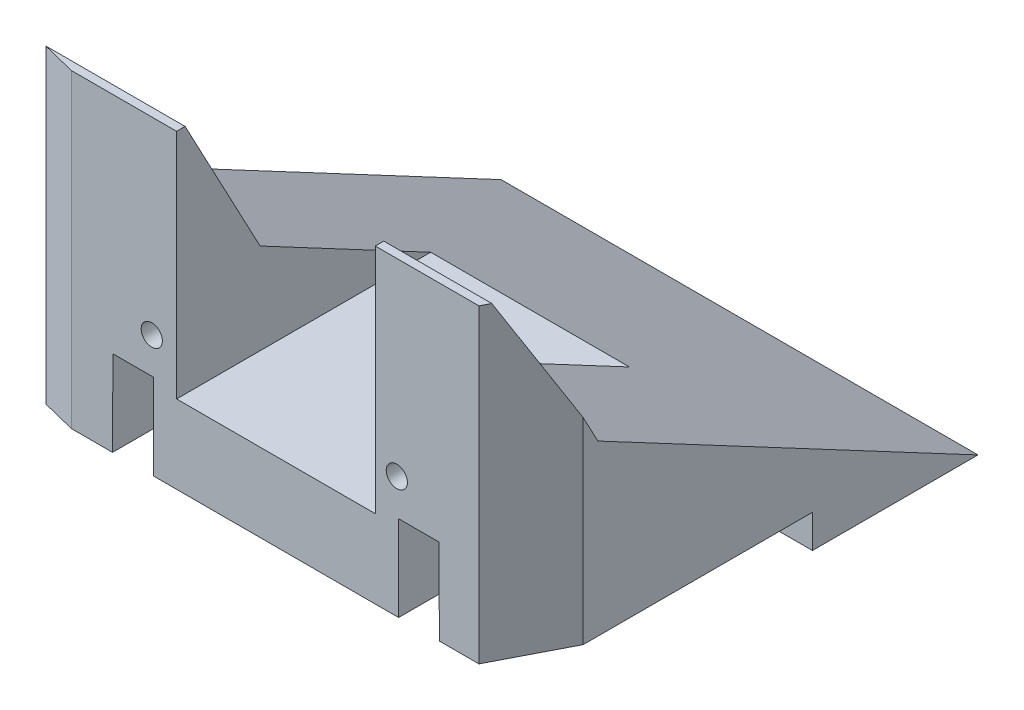
SolidWorks part; units mm, degrees
ref_plane "Alzado" through (0, 0, 0) normal (0, 0, 1) x (1, 0, 0)
ref_plane "Planta" through (0, 0, 0) normal (0, 1, 0) x (1, 0, 0)
ref_plane "Vista lateral" through (0, 0, 0) normal (1, 0, 0) x (0, 0, -1)
sketch "Croquis1" plane through (0, 0, 0) normal (1, 0, 0) x (0, 0, -1)
  line L1 (0, 0) -> (70, 0)
  line L2 (0, 0) -> (0, 51.82)
  line L3 (0, 51.82) -> (70, 51.82)
  line L4 (70, 0) -> (70, 51.82)
  dimension "D1" = 51.82
  dimension "D2" = 70
extrude "Saliente-Extruir1" add sketch "Croquis1" along normal blind 72
sketch "Croquis4" plane through (72, 0, 0) normal (1, 0, 0) x (0, 0, -1)
  line L0 (12.6084, 30.5157) -> (70, 0)
  line L1 (12.6084, 30.5157) -> (1.2807, 51.82)
  line L2 (70, 51.82) -> (0, 51.82) construction
  line L3 (70, 0) -> (70, 51.82)
  line L4 (70, 51.82) -> (1.2807, 51.82)
  line L5 (0, 0) -> (70, 0) construction
  dimension "D1" = 28
  dimension "D2" = 65
  dimension "D3" = 146
extrude "Cortar-Extruir1" cut sketch "Croquis4" against normal blind 72
sketch "Croquis5" plane through (0, 51.82, 0) normal (0, 1, 0) x (1, 0, 0)
  line L0 (72, 0) -> (51, 0) construction
  line L1 (72, 0) -> (0, 0) construction
  line L2 (0, 0) -> (21, 0) construction
  line L4 (51, 0) -> (21, 0)
  line L5 (51, 0) -> (51, 62)
  line L6 (51, 62) -> (21, 62)
  line L7 (21, 0) -> (21, 62)
  dimension "D1" = 62
extrude "Cortar-Extruir2" cut sketch "Croquis5" against normal blind 35
sketch "Croquis6" plane through (72, 0, 0) normal (1, 0, 0) x (0, 0, -1)
  line L1 (0, 0) -> (45, 0)
  line L2 (0, 0) -> (0, 5)
  line L3 (0, 5) -> (45, 5)
  line L4 (45, 0) -> (45, 5)
  dimension "D1" = 5
  dimension "D2" = 45
extrude "Cortar-Extruir3" cut sketch "Croquis6" against normal up to next
sketch "Croquis7" plane through (0, 51.82, 0) normal (0, 1, 0) x (1, 0, 0)
  line L0 (5.1034, 0) -> (0, 1.2807)
  line L4 (0, 0) -> (5.1034, 0)
  line L5 (21, 0) -> (0, 0) construction
  line L6 (0, 0) -> (0, 1.2807)
extrude "Cortar-Extruir4" cut sketch "Croquis7" against normal up to next
sketch "Croquis8" plane through (0, 51.82, 0) normal (0, 1, 0) x (1, 0, 0)
  line L0 (66.6483, 0) -> (72, 10.3828)
  line L1 (72, 0) -> (66.6483, 0)
  line L2 (72, 0) -> (51, 0) construction
  line L3 (72, 0) -> (72, 10.3828)
  line L4 (72, 1.2807) -> (72, 0) construction
extrude "Cortar-Extruir5" cut sketch "Croquis8" against normal up to next
sketch "Croquis18" plane through (0, 0, 0) normal (0, 0, 1) x (1, 0, 0)
  circle A0 centre (17.25, 23.32) radius 1.6
  circle A1 centre (54.25, 23.32) radius 1.6
extrude "Cortar-Extruir7" cut sketch "Croquis18" against normal blind 15
sketch "Croquis19" plane through (0, 5, 0) normal (0, -1, 0) x (1, 0, 0)
  line L0 (0, -45) -> (10, -45) construction
  line L1 (0, -45) -> (72, -45) construction
  line L2 (10, -45) -> (10, -35) construction
  line L3 (0, 0) -> (10, 0) construction
  line L5 (5.1034, 0) -> (66.6483, 0) construction
  line L6 (10, 0) -> (10, -10) construction
  line L7 (72, -45) -> (72, -35) construction
  line L8 (72, -45) -> (72, -10.3828) construction
  line L9 (72, -35) -> (62, -35) construction
  line L10 (62, -10) -> (71.8027, -10) construction
  line L11 (66.6483, 0) -> (72, -10.3828) construction
  line L12 (62, -10) -> (10, -10) construction
  line L13 (36, -10) -> (36, -35) construction
  circle A0 centre (10, -35) radius 1.75
  circle A1 centre (10, -10) radius 1.75
  circle A2 centre (62, -35) radius 1.75
  circle A3 centre (62, -10) radius 1.75
  circle A4 centre (36, -35) radius 2.5
  circle A5 centre (36, -10) radius 2.5
  dimension "D1" = 3.5
  dimension "D2" = 3.5
  dimension "D3" = 3.5
  dimension "D4" = 3.5
  dimension "D5" = 5
  dimension "D6" = 5
extrude "Cortar-Extruir8" cut sketch "Croquis19" against normal blind 6
sketch "Croquis21" plane through (0, 0, 0) normal (0, 0, 1) x (1, 0, 0)
  line L0 (11.3283, 5) -> (17.4783, 5)
  line L2 (36, 5) -> (36, 38.3764) construction
  line L4 (0, 5) -> (72, 5) construction
  line L9 (60.6717, 5) -> (54.5217, 5)
  line L11 (17.4783, 17.92) -> (17.4783, 5)
  line L12 (11.3783, 17.92) -> (11.3283, 5)
  line L13 (17.4783, 17.92) -> (11.3783, 17.92)
  line L15 (54.5217, 17.92) -> (54.5217, 5)
  line L16 (60.6217, 17.92) -> (60.6717, 5)
  line L17 (54.5217, 17.92) -> (60.6217, 17.92)
  dimension "D1" = 12.92
  dimension "D2" = 6.15
extrude "Cortar-Extruir10" cut sketch "Croquis21" against normal blind 10
sketch "Croquis22" plane through (0, 29.0163, -15.4282) normal (0, 0.8829, -0.4695) x (1, 0, 0)
